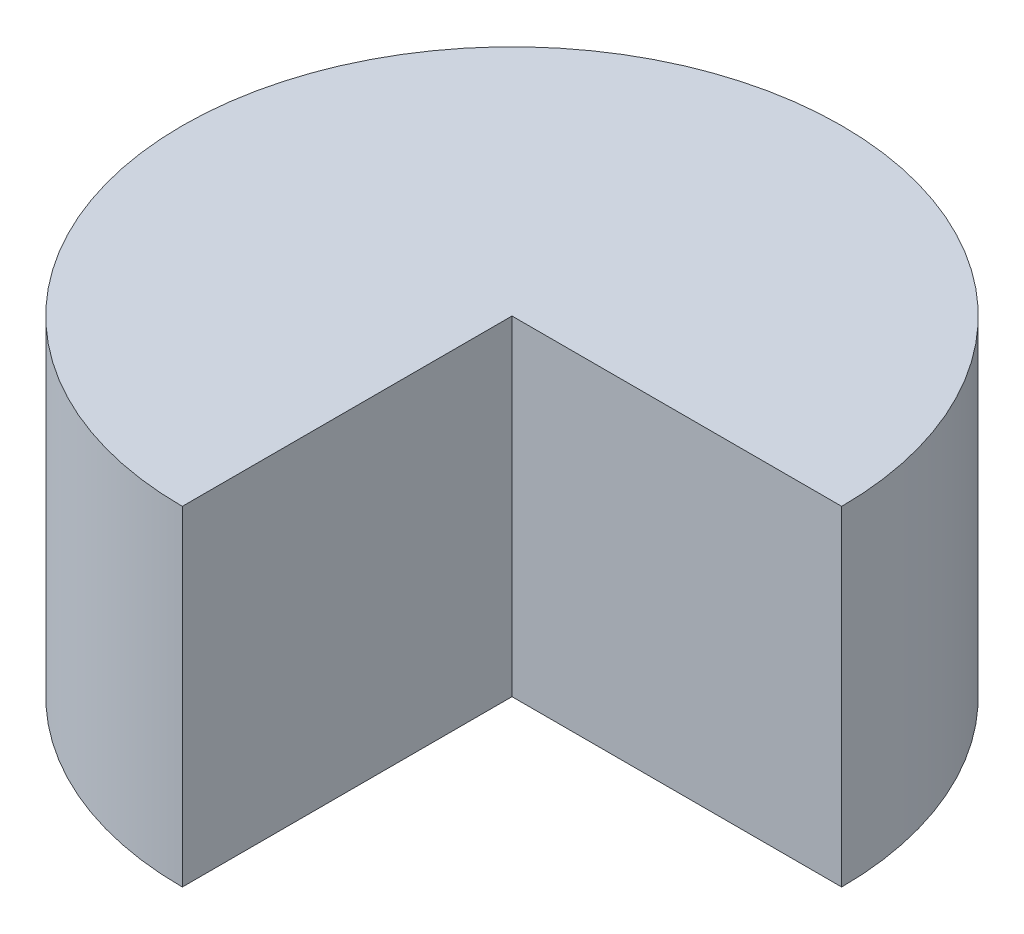
SolidWorks part; units mm, degrees
ref_plane "Front Plane" through (0, 0, 0) normal (0, 0, 1) x (1, 0, 0)
ref_plane "Top Plane" through (0, 0, 0) normal (0, 1, 0) x (1, 0, 0)
ref_plane "Right Plane" through (0, 0, 0) normal (1, 0, 0) x (0, 0, -1)
sketch "Sketch1" plane through (0, 0, 0) normal (0, 1, 0) x (1, 0, 0)
  line L0 (0, 0) -> (80, 0)
  line L2 (0, 0) -> (0, -80)
  arc A1 (0, -80) -> (80, 0) centre (0, 0) cw
  point P4 (0, 0)
  point P5 (0, 0)
  point P6 (0, 0)
  dimension "D1" = 80
extrude "Boss-Extrude1" add sketch "Sketch1" along normal blind 80 contours A1 L0 L2
sketch "Bend-Lines1" [suppressed] plane through (0, 0, 0) normal (0, 1, 0) x (1, 0, 0)
sketch "Bounding-Box1" [suppressed] plane through (0, 0, 0) normal (0, 1, 0) x (1, 0, 0)
